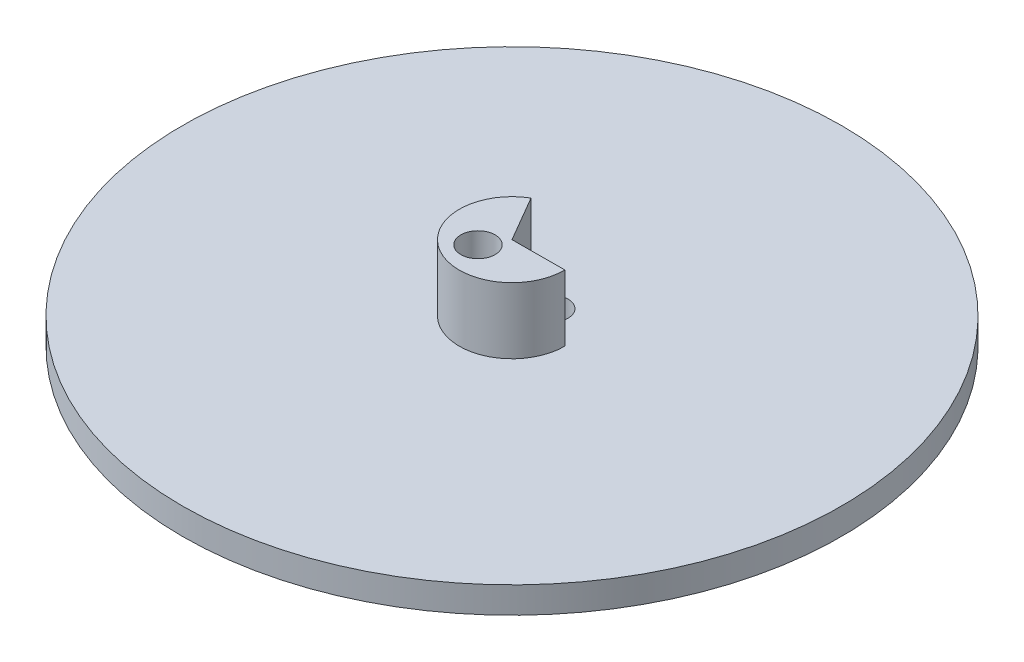
SolidWorks part; units mm, degrees
ref_plane "Front Plane" through (0, 0, 0) normal (0, 0, 1) x (1, 0, 0)
ref_plane "Top Plane" through (0, 0, 0) normal (0, 1, 0) x (1, 0, 0)
ref_plane "Right Plane" through (0, 0, 0) normal (1, 0, 0) x (0, 0, -1)
sketch "Sketch1" plane through (0, 0, 0) normal (0, 1, 0) x (1, 0, 0)
  circle A0 centre (0, 0) radius 63.5
extrude "Boss-Extrude1" add sketch "Sketch1" along normal blind 5.08
sketch "Sketch2" plane through (0, 5.08, 0) normal (0, 1, 0) x (1, 0, 0)
  line L0 (-5.1133, 8.7795) -> (0, 0)
  line L1 (0, 0) -> (10.1599, 0.0385)
  arc A0 (10.1599, 0.0385) -> (-5.1133, 8.7795) centre (0, 0) cw
extrude "Boss-Extrude2" add sketch "Sketch2" along normal blind 12.7
sketch "Sketch5" plane through (0, 5.08, 0) normal (0, 1, 0) x (1, 0, 0)
  circle A0 centre (2.6284, 5.0211) radius 3.175
extrude "Cut-Extrude1" cut sketch "Sketch5" against normal through all
sketch "Sketch6" plane through (0, 17.78, 0) normal (0, 1, 0) x (1, 0, 0)
  circle A0 centre (-2.4327, -4.1223) radius 3.302
extrude "Cut-Extrude2" cut sketch "Sketch6" against normal through all
